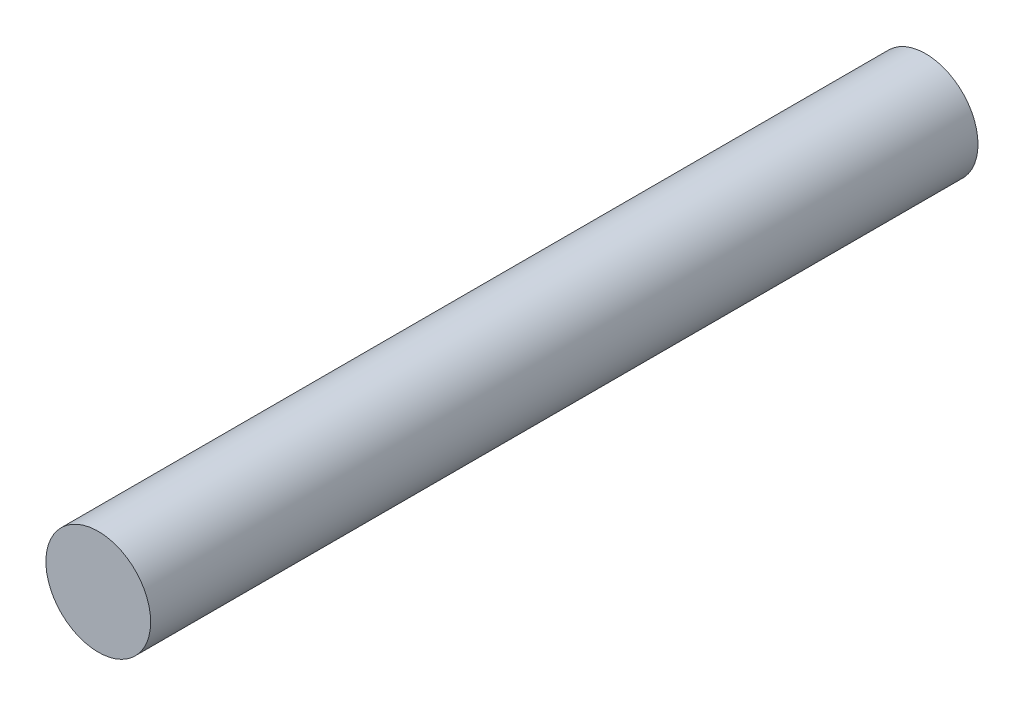
SolidWorks part; units mm, degrees
ref_plane "Front Plane" through (0, 0, 0) normal (0, 0, 1) x (1, 0, 0)
ref_plane "Top Plane" through (0, 0, 0) normal (0, 1, 0) x (1, 0, 0)
ref_plane "Right Plane" through (0, 0, 0) normal (1, 0, 0) x (0, 0, -1)
sketch "Sketch1" plane through (0, 0, 0) normal (0, 0, 1) x (1, 0, 0)
  circle A0 centre (0, 0) radius 2
  dimension "D1" = 4
extrude "Boss-Extrude1" add sketch "Sketch1" along normal mid plane 31.6
